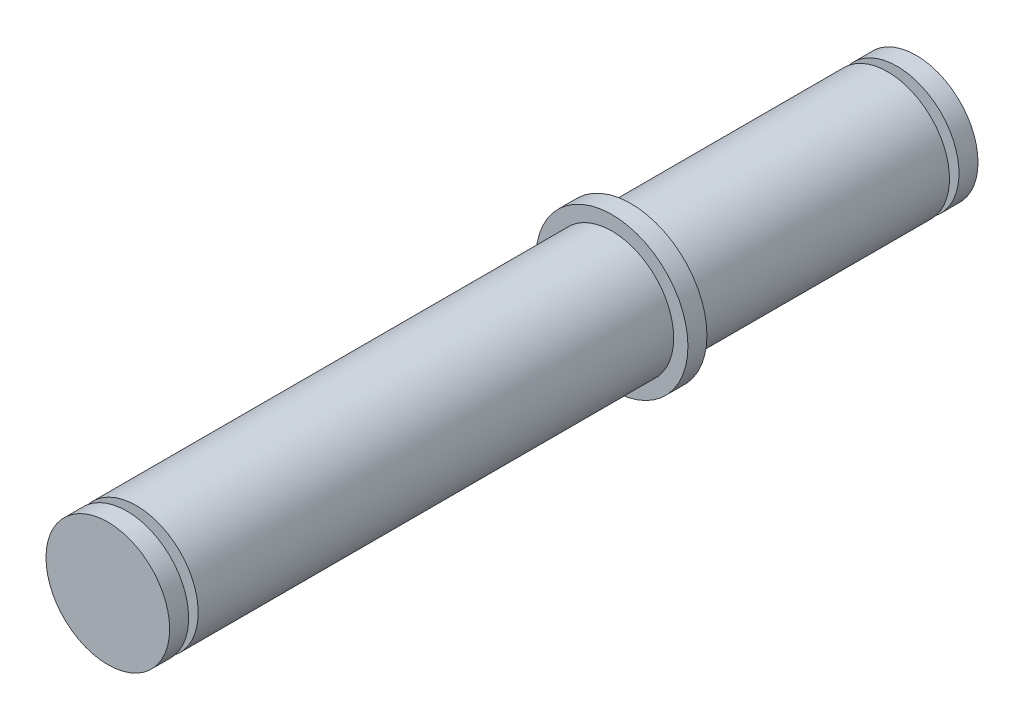
SolidWorks part; units mm, degrees
material "PA Type 6"
ref_plane "Front Plane" through (0, 0, 0) normal (0, 0, 1) x (1, 0, 0)
ref_plane "Top Plane" through (0, 0, 0) normal (0, 1, 0) x (1, 0, 0)
ref_plane "Right Plane" through (0, 0, 0) normal (1, 0, 0) x (0, 0, -1)
sketch "Sketch1" plane through (0, 0, 0) normal (0, 0, 1) x (1, 0, 0)
  circle A0 centre (0, 0) radius 6.5
  dimension "D1" = 13
extrude "Boss-Extrude1" add sketch "Sketch1" along normal mid plane 85
ref_plane "Plane1" through (0, 0, -12.5) normal (0, 0, 1) x (1, 0, 0)
sketch "Sketch2" plane through (0, 0, -12.5) normal (0, 0, 1) x (1, 0, 0)
  circle A0 centre (0, 0) radius 8
  dimension "D1" = 16
extrude "Boss-Extrude2" add sketch "Sketch2" along normal blind 2
ref_plane "Plane2" through (0, 0, -40.5) normal (0, 0, -1) x (-1, 0, 0)
sketch "Sketch3" plane through (0, 0, -40.5) normal (0, 0, -1) x (-1, 0, 0)
  circle A0 centre (0, 0) radius 4.5
  circle A1 centre (0, 0) radius 6.5 construction
  circle A2 centre (0, 0) radius 6.5
  dimension "D1" = 9
extrude "Cut-Extrude1" cut sketch "Sketch3" against normal blind 1
mirror "Mirror1" about plane through (0, 0, 0) normal (0, 0, 1) of "Cut-Extrude1"
